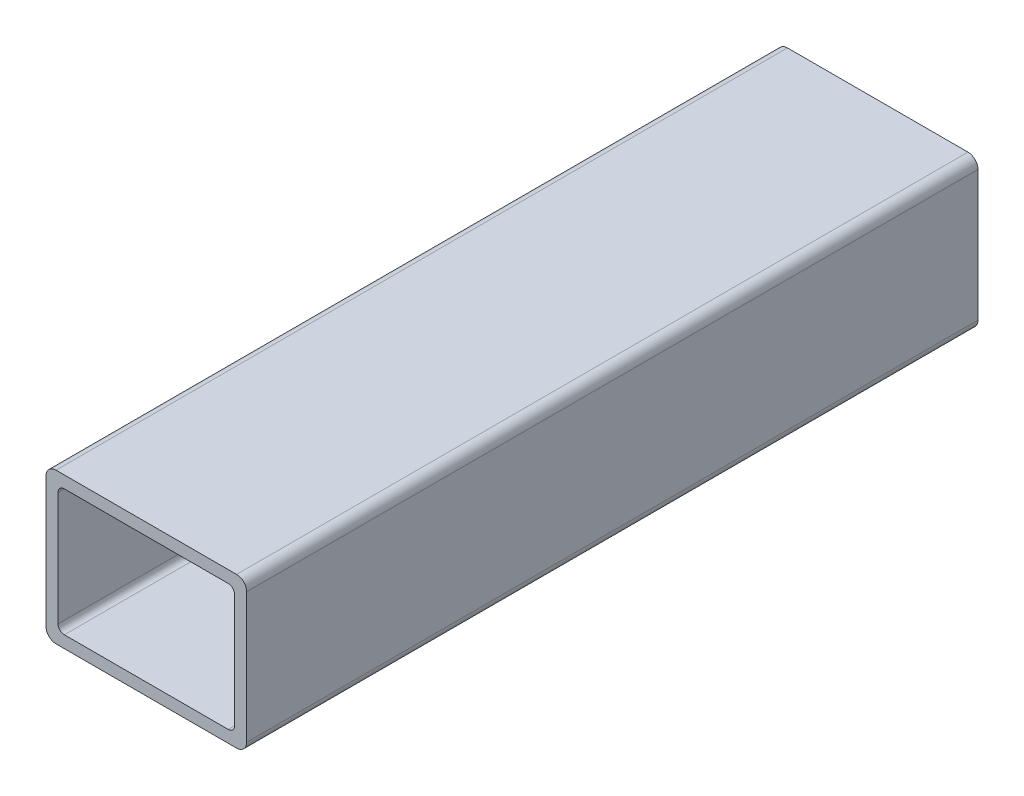
SolidWorks part; units mm, degrees
material "Plain Carbon Steel"
ref_plane "Front" through (0, 0, 0) normal (0, 0, 1) x (1, 0, 0)
ref_plane "Top" through (0, 0, 0) normal (0, 1, 0) x (1, 0, 0)
ref_plane "Right" through (0, 0, 0) normal (1, 0, 0) x (0, 0, -1)
sketch "Sketch1" plane through (0, 0, 0) normal (0, 0, 1) x (1, 0, 0)
  line L0 (-22.352, 0) -> (-25.4, 0) construction
  line L1 (22.86, -19.05) -> (-22.86, -19.05)
  line L2 (25.4, -16.51) -> (25.4, 16.51)
  line L3 (22.86, 19.05) -> (-22.86, 19.05)
  line L4 (-25.4, -16.51) -> (-25.4, 16.51)
  line L5 (25.4, -19.05) -> (-25.4, 19.05) construction
  line L6 (25.4, 19.05) -> (-25.4, -19.05) construction
  line L7 (20.7518, 16.002) -> (-20.7518, 16.002)
  line L8 (22.352, 14.4018) -> (22.352, -14.4018)
  line L9 (20.7518, -16.002) -> (-20.7518, -16.002)
  line L10 (-22.352, 14.4018) -> (-22.352, -14.4018)
  line L11 (22.352, 16.002) -> (-22.352, -16.002) construction
  line L12 (22.352, -16.002) -> (-22.352, 16.002) construction
  line L13 (0, -16.002) -> (0, -19.05) construction
  line L14 (22.352, -14.4018) -> (22.352, -19.05) construction
  line L16 (22.352, -19.05) -> (25.4, -19.05) construction
  arc A0 (-20.7518, -16.002) -> (-22.352, -14.4018) centre (-20.7518, -14.4018) cw
  arc A1 (22.352, -14.4018) -> (20.7518, -16.002) centre (20.7518, -14.4018) cw
  arc A2 (20.7518, 16.002) -> (22.352, 14.4018) centre (20.7518, 14.4018) cw
  arc A3 (-20.7518, 16.002) -> (-22.352, 14.4018) centre (-20.7518, 14.4018) ccw
  arc A4 (22.86, -19.05) -> (25.4, -16.51) centre (22.86, -16.51) ccw
  arc A5 (25.4, 16.51) -> (22.86, 19.05) centre (22.86, 16.51) ccw
  arc A6 (-22.86, 19.05) -> (-25.4, 16.51) centre (-22.86, 16.51) ccw
  arc A7 (-22.86, -19.05) -> (-25.4, -16.51) centre (-22.86, -16.51) cw
  point P0 (0, 0)
  point P6 (0, 0)
  dimension "D2" = 1.6002
  dimension "D3" = 2.54
sketch "Sketch2" plane through (0, 0, 0) normal (1, 0, 0) x (0, 0, -1)
  line L0 (-152.4, 0) -> (152.4, 0) construction
  dimension "Length" = 304.8
ref_plane "Plane1" through (25.4, 0, 0) normal (1, 0, 0) x (0, 0, -1)
sketch "Sketch5" plane through (25.4, 0, 0) normal (1, 0, 0) x (0, 0, -1)
  line L0 (-152.4, 19.05) -> (-152.4, -19.05) construction
  line L1 (152.4, 19.05) -> (152.4, -19.05) construction
sketch "Sketch4" plane through (0, 0, 0) normal (0, 0, 1) x (1, 0, 0)
  line L0 (25.4, -16.51) -> (25.4, 16.51) construction
  line L1 (22.86, 19.05) -> (-22.86, 19.05) construction
  line L2 (-25.4, -16.51) -> (-25.4, 16.51) construction
  line L3 (22.86, -19.05) -> (-22.86, -19.05) construction
  line L4 (22.352, 14.4018) -> (22.352, -14.4018) construction
  line L5 (20.7518, -16.002) -> (-20.7518, -16.002) construction
  line L6 (-22.352, 14.4018) -> (-22.352, -14.4018) construction
  line L7 (20.7518, 16.002) -> (-20.7518, 16.002) construction
  line L8 (25.4, -16.51) -> (25.4, 16.51)
  line L9 (22.86, 19.05) -> (-22.86, 19.05)
  line L10 (-25.4, -16.51) -> (-25.4, 16.51)
  line L11 (22.86, -19.05) -> (-22.86, -19.05)
  line L12 (22.352, 14.4018) -> (22.352, -14.4018)
  line L13 (20.7518, -16.002) -> (-20.7518, -16.002)
  line L14 (-22.352, 14.4018) -> (-22.352, -14.4018)
  line L15 (20.7518, 16.002) -> (-20.7518, 16.002)
  arc A0 (25.4, 16.51) -> (22.86, 19.05) centre (22.86, 16.51) ccw construction
  arc A1 (-22.86, 19.05) -> (-25.4, 16.51) centre (-22.86, 16.51) ccw construction
  arc A2 (-25.4, -16.51) -> (-22.86, -19.05) centre (-22.86, -16.51) ccw construction
  arc A3 (22.86, -19.05) -> (25.4, -16.51) centre (22.86, -16.51) ccw construction
  arc A4 (20.7518, -16.002) -> (22.352, -14.4018) centre (20.7518, -14.4018) ccw construction
  arc A5 (-22.352, -14.4018) -> (-20.7518, -16.002) centre (-20.7518, -14.4018) ccw construction
  arc A6 (-20.7518, 16.002) -> (-22.352, 14.4018) centre (-20.7518, 14.4018) ccw construction
  arc A7 (22.352, 14.4018) -> (20.7518, 16.002) centre (20.7518, 14.4018) ccw construction
  arc A8 (25.4, 16.51) -> (22.86, 19.05) centre (22.86, 16.51) ccw
  arc A9 (-22.86, 19.05) -> (-25.4, 16.51) centre (-22.86, 16.51) ccw
  arc A10 (-25.4, -16.51) -> (-22.86, -19.05) centre (-22.86, -16.51) ccw
  arc A11 (22.86, -19.05) -> (25.4, -16.51) centre (22.86, -16.51) ccw
  arc A12 (20.7518, -16.002) -> (22.352, -14.4018) centre (20.7518, -14.4018) ccw
  arc A13 (-22.352, -14.4018) -> (-20.7518, -16.002) centre (-20.7518, -14.4018) ccw
  arc A14 (-20.7518, 16.002) -> (-22.352, 14.4018) centre (-20.7518, 14.4018) ccw
  arc A15 (22.352, 14.4018) -> (20.7518, 16.002) centre (20.7518, 14.4018) ccw
extrude "Boss-Extrude1" add sketch "Sketch4" along normal blind 185.2193
equation "\"D3@Sketch1\"=\"Outside Width@Sketch1\"*.05"
equation "\"D2@Sketch1\"=\"D1@Sketch1\"*.05"
